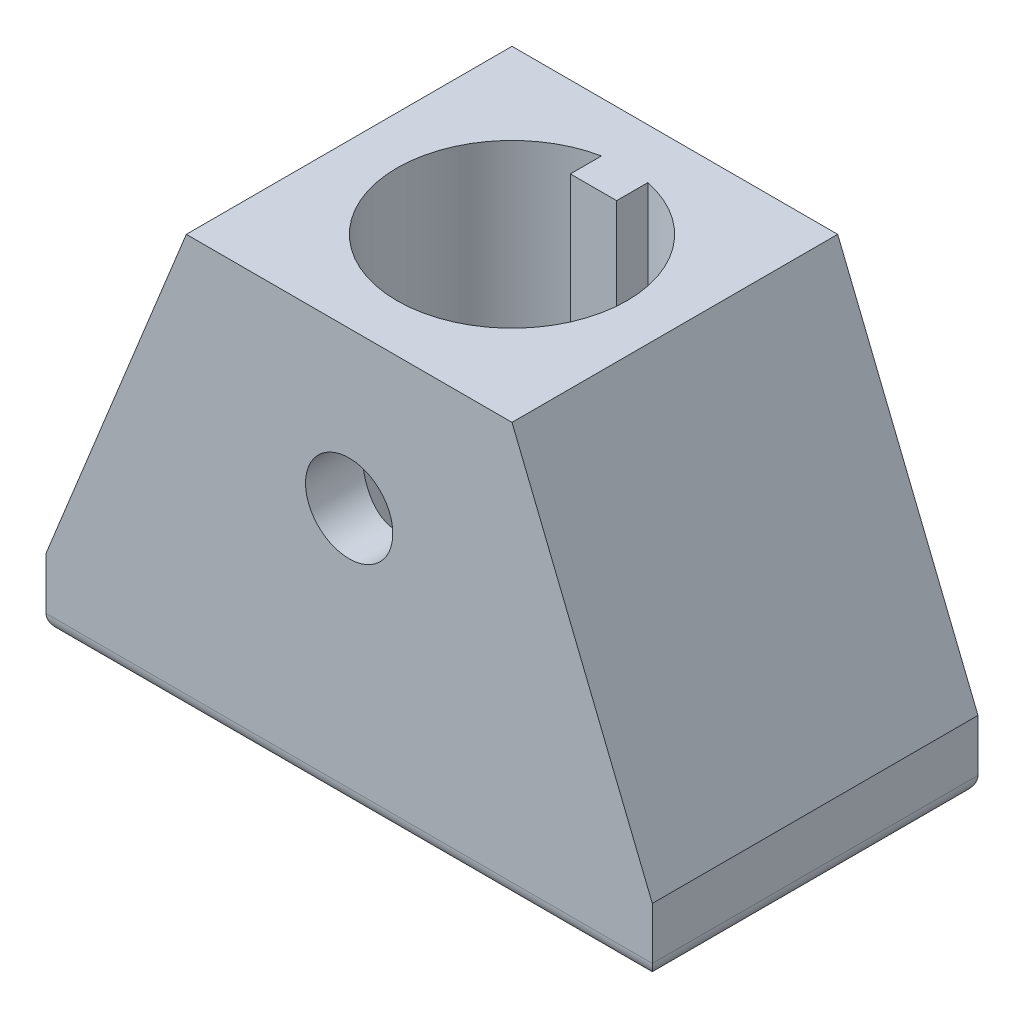
SolidWorks part; units mm, degrees
ref_plane "Front Plane" through (0, 0, 0) normal (0, 0, 1) x (1, 0, 0)
ref_plane "Top Plane" through (0, 0, 0) normal (0, 1, 0) x (1, 0, 0)
ref_plane "Right Plane" through (0, 0, 0) normal (1, 0, 0) x (0, 0, -1)
sketch "Sketch1" plane through (0, 0, 0) normal (0, 1, 0) x (1, 0, 0)
  line L0 (-1.335, 6.5044) -> (-1.335, 4.7044)
  line L1 (-1.335, 4.7044) -> (1.335, 4.7044)
  line L2 (1.335, 4.7044) -> (1.335, 6.5044)
  line L4 (-9.4, -9.4) -> (9.4, -9.4)
  line L5 (-9.4, -9.4) -> (-9.4, 9.4)
  line L6 (-9.4, 9.4) -> (9.4, 9.4)
  line L7 (9.4, -9.4) -> (9.4, 9.4)
  line L8 (-9.4, -9.4) -> (9.4, 9.4) construction
  line L9 (-9.4, 9.4) -> (9.4, -9.4) construction
  arc A1 (-1.335, 6.5044) -> (1.335, 6.5044) centre (0, 0) ccw
  dimension "D1" = 13.28
  dimension "D2" = 18.8
  dimension "D3" = 1.8
  dimension "D4" = 2.67
  dimension "D5" = 1.335
  dimension "D6" = 18.8
extrude "Boss-Extrude1" add sketch "Sketch1" along normal blind 20
sketch "Sketch5" plane through (0, 0, -4.7044) normal (0, 0, 1) x (1, 0, 0)
  line L0 (1.335, 20) -> (-1.335, 20) construction
  circle A0 centre (-0.0003, 11) radius 2.52
  point P2 (0, 20)
  dimension "D1" = 5.04
  dimension "D2" = 9
extrude "Cut-Extrude3" cut sketch "Sketch5" along normal blind 15
sketch "Sketch6" plane through (0, 0, 0) normal (0, -1, 0) x (1, 0, 0)
  line L1 (17.5, -9.4) -> (-17.5, -9.4)
  line L2 (17.5, -9.4) -> (17.5, 9.4)
  line L3 (17.5, 9.4) -> (-17.5, 9.4)
  line L4 (-17.5, -9.4) -> (-17.5, 9.4)
  line L5 (17.5, -9.4) -> (-17.5, 9.4) construction
  line L6 (17.5, 9.4) -> (-17.5, -9.4) construction
  point P0 (0, 0)
  dimension "D1" = 18.8
  dimension "D2" = 35
extrude "Boss-Extrude2" add sketch "Sketch6" along normal blind 4
sketch "Sketch7" plane through (0, 0, 9.4) normal (0, 0, 1) x (1, 0, 0)
  line L0 (-9.4, 20) -> (-9.4, 0)
  line L1 (-9.4, 0) -> (-17.5, 0)
  line L2 (-17.5, 0) -> (-9.4, 20)
  line L3 (9.4, 0) -> (17.5, 0)
  line L4 (17.5, 0) -> (9.4, 20)
  line L5 (9.4, 20) -> (9.4, 0)
extrude "Boss-Extrude3" add sketch "Sketch7" against normal up to surface (18.8 mm away) up to face at (-1.0125, 6.5, -9.4)
fillet "Fillet4" radius 1 4 edges at (17.5, -4, 0) (0, -4, -9.4) (-17.5, -4, 0) (0, -4, 9.4)
sketch "Sketch8" plane through (0, 0, 0) normal (0, 1, 0) x (1, 0, 0)
  line L0 (1.335, 4.7044) -> (-1.335, 4.7044) construction
  line L1 (1.335, 6.5044) -> (1.335, 4.7044) construction
  line L2 (-1.335, 4.7044) -> (-1.335, 6.5044) construction
  line L3 (1.335, 4.7044) -> (-1.335, 4.7044)
  line L4 (1.335, 6.5044) -> (1.335, 4.7044)
  line L5 (-1.335, 4.7044) -> (-1.335, 6.5044)
  arc A0 (-1.335, 6.5044) -> (1.335, 6.5044) centre (0, 0) ccw construction
  arc A1 (-1.335, 6.5044) -> (1.335, 6.5044) centre (0, 0) ccw
extrude "Cut-Extrude4" cut sketch "Sketch8" against normal blind 4
fillet "Fillet5" radius 0.5 4 edges at (-1.335, -4, -5.6044) (0, -4, -4.7044) (1.335, -4, -5.6044) (0, -4, 6.64)
equation "\"CageLeftBottomEdge\"=22.11mm"
equation "\"CageLeftTopEdge\"=22.11mm"
equation "\"CageRightBottomEdge\"=21.63mm"
equation "\"CageRightTopEdge\"=21.63mm"
equation "\"CageHeight\"=86.04mm"
equation "\"CageLength\"=73.76mm"
equation "\"CageTopScrewClearance\"=10mm"
equation "\"CageBottomScrewClearance\"=25mm"
equation "\"CageLeftTopDepth\"= 11.65mm"
equation "\"CageLeftBottomDepth\"=11.11mm"
equation "\"CageLeftTopHeight\"=8.56175mm"
equation "\"CageLeftBottomHeight\"=16mm"
equation "\"CageRightTopDepth\"= 11.05mm"
equation "\"CageRightBottomDepth\"=10.58mm"
equation "\"CageRightTopHeight\"=9.6mm"
equation "\"CageRightBottomHeight\"=15.49mm"
equation "\"CageLeftTopChannelDepth\"=2.41908mm"
equation "\"CageLeftBottomChannelDepth\"=2.588mm"
equation "\"CageLeftChannelHeight\"=11.7mm"
equation "\"CageRightTopChannelDepth\"=2.32mm"
equation "\"CageRightBottomChannelDepth\"=2.318mm"
equation "\"CageRightChannelHeight\"=10mm"
equation "\"CageChanRelHeight\"=23.99mm"
equation "\"CageChanRelDepth\"=5.492mm"
equation "\"CageChamberRadius\"=16.261mm"
equation "\"CageScrewDiameter\"=4.8mm"
equation "\"CageSetScrewDiameter\"=3.5mm"
equation "\"CageAxleRadius\"=6.639mm"
equation "\"CageAxleKeyHeight\"=1.619mm"
equation "\"CageAxleKeyWidth\"=2.662mm"
equation "\"CageHoseWindowWidth\"=16.29mm"
equation "\"CageHoseWindowHeight\"=26.5mm"
equation "\"CageHoseWindow-Edge\"=8.89mm"
equation "\"CageScrew-VerticalEdge\"=5.0mm"
equation "\"CageScrew-HorizontalEdge\"=7.5mm"
equation "\"CageScrew-HoseCornerScrewEdge\"=4.45mm"
equation "\"CageAxle-BottomEdge\"=56.05mm"
equation "\"CageAxle-FrontEdge\"=46.03mm"
equation "\"CageBackSetScrew-Axle\"=40mm"
equation "\"CageFrontSetScrew-Axle\"=22mm"
equation "\"CageVelocityWindow-BackEdge\"=34.8mm"
equation "\"CageVelocityWindow-BottomEdge\"=27.55mm"
equation "\"CageVelocityWindowHeight\"=22.29mm"
equation "\"CageVelocityWindowWidth\"=12.61mm"
equation "\"TriggerSlot-BottomEdge\"=6.35mm"
equation "\"TriggerSlot-FrontEdge\"=15mm"
equation "\"TriggerSlotSize\"=6.7mm"
equation "\"TriggerRackOffset\"=6mm"
equation "\"TriggerSlotSizeInt\"=.25in"
equation "\"MotorMountLegLength\"=.25in"
equation "\"GearOffset\"=.264907in"
equation "\"TriggerSlotSpacing\"=.25in"
equation "\"TriggerMiniSlotWidth\"=3.5mm"
equation "\"TriggerRackWidth\"=6.5mm"
equation "\"pandiscradius\"=14in"
equation "\"towermaterialwidth\"=.25in"
equation "\"towerslotlength\"=.5in"
equation "\"towermarkerspace\"=5in"
equation "\"towerslothorizoffset\"=1in"
equation "\"towerslothorizspacing\"=2in"
equation "\"towerslotvertoffset\"=3in"
equation "\"towerslotvertspacing\"=1in"
equation "\"towerheight\"=12in"
equation "\"towerupslot\"=1in"
equation "\"toweraxle\"=.5in"
equation "\"stepperouterrad\"=10mm"
equation "\"stepperscrewsize\"=3.45mm"
equation "\"stepperscrewc2c\"=49.5mm"
equation "\"stepperdepthoffset\"=24mm"
equation "\"stepperhorizoffset\"=22.91mm"
equation "\"shaftslotOD\"=18.8mm"
equation "\"shaftslotID\"=13.28mm"
equation "\"shaftkeywidth\"=2.67mm"
equation "\"shaftkeydepth\"=1.8mm"
equation "\"shaftcollartotaldepth\"=9.71mm"
equation "\"shaftsquaredepth\"=6mm"
equation "\"shaftsetscrewsize\"=3.5mm"
equation "\"shaftkeytightdepth\"=1.85mm"
equation "\"shaftslottightID\"=12.78mm"
equation "\"D3@Sketch1\"=\"shaftkeydepth\""
equation "\"D4@Sketch1\"=\"shaftkeywidth\""
equation "\"D5@Sketch1\"=\"shaftkeywidth\"/2"
equation "\"D1@Sketch1\"=\"shaftslotID\""
equation "\"D6@Sketch1\"=\"shaftslotOD\""
equation "\"D2@Sketch1\"=\"shaftslotOD\""
equation "\"D1@Sketch6\"=\"shaftslotOD\""
equation "\"cagecollartotaldepth\"=20mm"
equation "\"D1@Boss-Extrude1\"=\"cagecollartotaldepth\""
equation "\"D1@Sketch5\"=\"BrassInsertDiameter\""
equation "\"D2@Sketch5\"=\"shaftsetscrewoffset\""
equation "\"cagecollartotalwidth\"=35mm"
equation "\"D2@Sketch6\"=\"cagecollartotalwidth\""
equation "\"cagecollarbasedepth\"=4mm"
equation "\"D1@Boss-Extrude2\"=\"cagecollarbasedepth\""
equation "\"shaftsetscrewoffset\"=9mm"
equation "\"gearhubintdiam\"=30mm"
equation "\"gearhubintwid\"=12.21mm"
equation "\"towerspeedwidth\"=2in"
equation "\"towerspeedheight\"=8in"
equation "\"towerspeedgap\"=2in"
equation "\"stepperaxleflat\"=.037in"
equation "\"stepperaxlerad\"=0.11811024in"
equation "\"ajaxaxlesize\"=3.87mm"
equation "\"ajaxinnercut\"=2.3mm"
equation "\"ajaxwidth\"=6.1mm"
equation "\"ajaxdiametral\"=25.8854"
equation "\"ajaxcutoutdepth\"=2.3mm"
equation "\"ajax4020gap\"=29.5mm"
equation "\"ajax4010gap\"=24.5mm"
equation "\"ajax20hubbuffer\"=6.1mm"
equation "\"ajax20hubholeoffset\"=.19685in"
equation "\"ajax20hubholesize\"=.059055in"
equation "\"ajax20cutoutint\"=13.4mm"
equation "\"ajax40hubholesize\"=7.21mm"
equation "\"ajax40hubholeoffset\"=10mm"
equation "\"ajax40hubbuffer\"=8.9mm"
equation "\"ajax40cutoutint\"=32.6mm"
equation "\"bearingpandiscrad\"=6.8in"
equation "\"bearingpandiscang\"=48.75deg"
equation "\"bearingclearholedist\"=4.7345in"
equation "\"bearingclearholesize\"=.5in"
equation "\"bearingclearholeang\"=22.5deg"
equation "\"bearingmountholedist\"=4.25in"
equation "\"bearingwirehole\"=1.5in"
equation "\"no6diam\"=.146in"
equation "\"shortconangle\"=20deg"
equation "\"shortconlen\"=.875in"
equation "\"longconlen\"=1.25in"
equation "\"longconangle\"=15deg"
equation "\"vigorwidth\"= 0.472441in"
equation "\"vigorflangewidth\"= 0.731102in"
equation "\"vigorflangelength\"= 0.131102in"
equation "\"vigorscrewsize\"= 0.066535in"
equation "\"vigorholeoffsetwid\"= 0.0646653in"
equation "\"vigorholeoffsetlen\"= 0.065551in"
equation "\"vigorflangedepth\"= 0.0901575in"
equation "\"vigordiscdepth\"= 0.0492126in"
equation "\"vigormotordepth\"= 1.12362in"
equation "\"vigortipdepth\"= 0.259055in"
equation "\"vigoraxlewidth\"= 0.173622in"
equation "\"vigorcutlen\"= 0.0480315in"
equation "\"vigoraxledepth\"= 0.159055in"
equation "\"BrassInsertDiameter\"=5.04mm"
